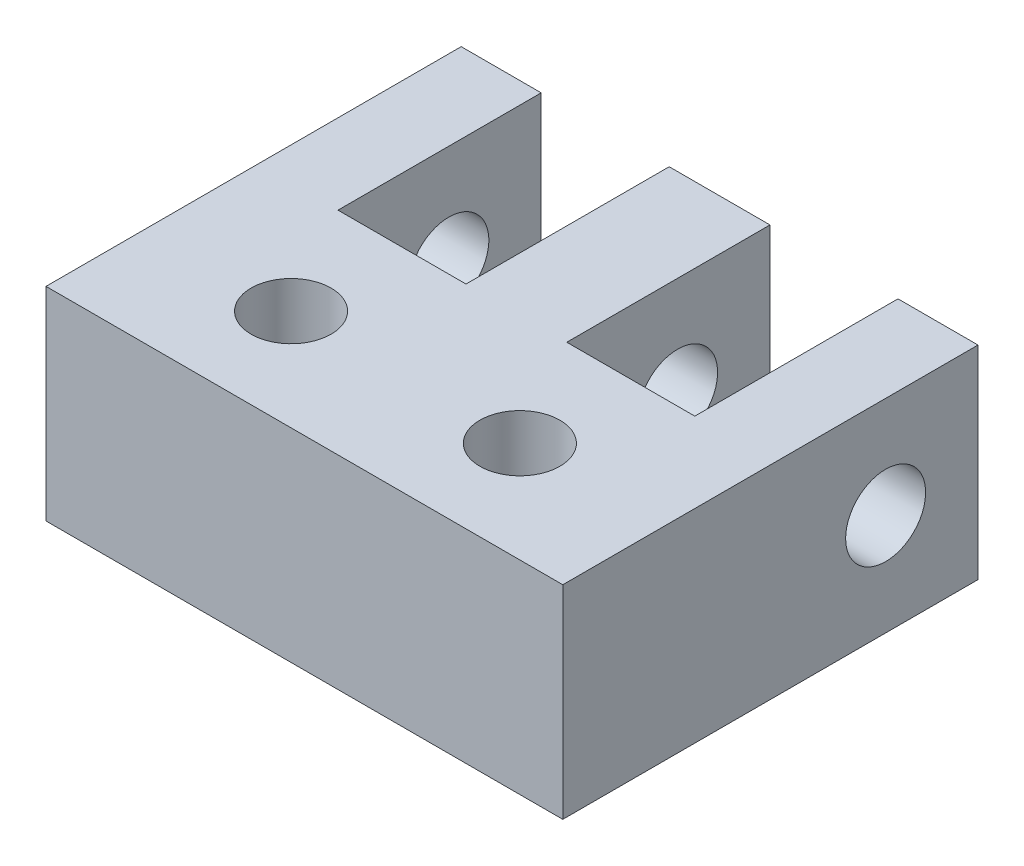
SolidWorks part; units mm, degrees
ref_plane "Front Plane" through (0, 0, 0) normal (0, 0, 1) x (1, 0, 0)
ref_plane "Top Plane" through (0, 0, 0) normal (0, 1, 0) x (1, 0, 0)
ref_plane "Right Plane" through (0, 0, 0) normal (1, 0, 0) x (0, 0, -1)
sketch "Sketch2" plane through (0, 0, 0) normal (0, 1, 0) x (1, 0, 0)
  line L0 (-8.075, 9.8163) -> (-5.575, 9.8163)
  line L2 (-8.075, 9.8163) -> (-8.075, -3.1587)
  line L3 (-8.075, -3.1587) -> (8.075, -3.1587)
  line L4 (8.075, 9.8163) -> (8.075, -3.1587)
  line L5 (-5.575, 9.8163) -> (-5.575, 3.4663)
  line L6 (-5.575, 3.4663) -> (-1.575, 3.4663)
  line L7 (-1.575, 3.4663) -> (-1.575, 9.8163)
  line L9 (0, 6.6413) -> (0, -3.1587) construction
  line L10 (1.575, 3.4663) -> (1.575, 9.8163)
  line L11 (5.575, 3.4663) -> (1.575, 3.4663)
  line L12 (5.575, 9.8163) -> (5.575, 3.4663)
  line L13 (8.075, 9.8163) -> (5.575, 9.8163)
  line L14 (-1.575, 9.8163) -> (1.575, 9.8163)
  line L15 (-3.575, 3.4663) -> (-3.575, 0) construction
  line L16 (3.575, 3.4663) -> (3.575, -3.1587) construction
  circle A0 centre (-3.575, 0) radius 1.25
  circle A1 centre (3.575, 0) radius 1.25
  point P0 (0, 0)
  dimension "D6" = 2.5
  dimension "D1" = 2.5
  dimension "D2" = 6.35
  dimension "D3" = 4
  dimension "D4" = 3.4663
  dimension "D5" = 16.15
  dimension "D7" = 6.625
  dimension "D8" = 6.35
extrude "Boss-Extrude1" add sketch "Sketch2" along normal blind 6.35
sketch "Sketch4" plane through (-8.075, 0, 0) normal (-1, 0, 0) x (0, 0, 1)
  line L0 (-9.8163, 3.175) -> (-5.0295, 3.175) construction
  line L2 (-9.8163, 6.35) -> (-9.8163, 0) construction
  circle A0 centre (-6.9297, 3.1811) radius 1.25
  dimension "D1" = 2.5
extrude "Cut-Extrude1" cut sketch "Sketch4" against normal through all
